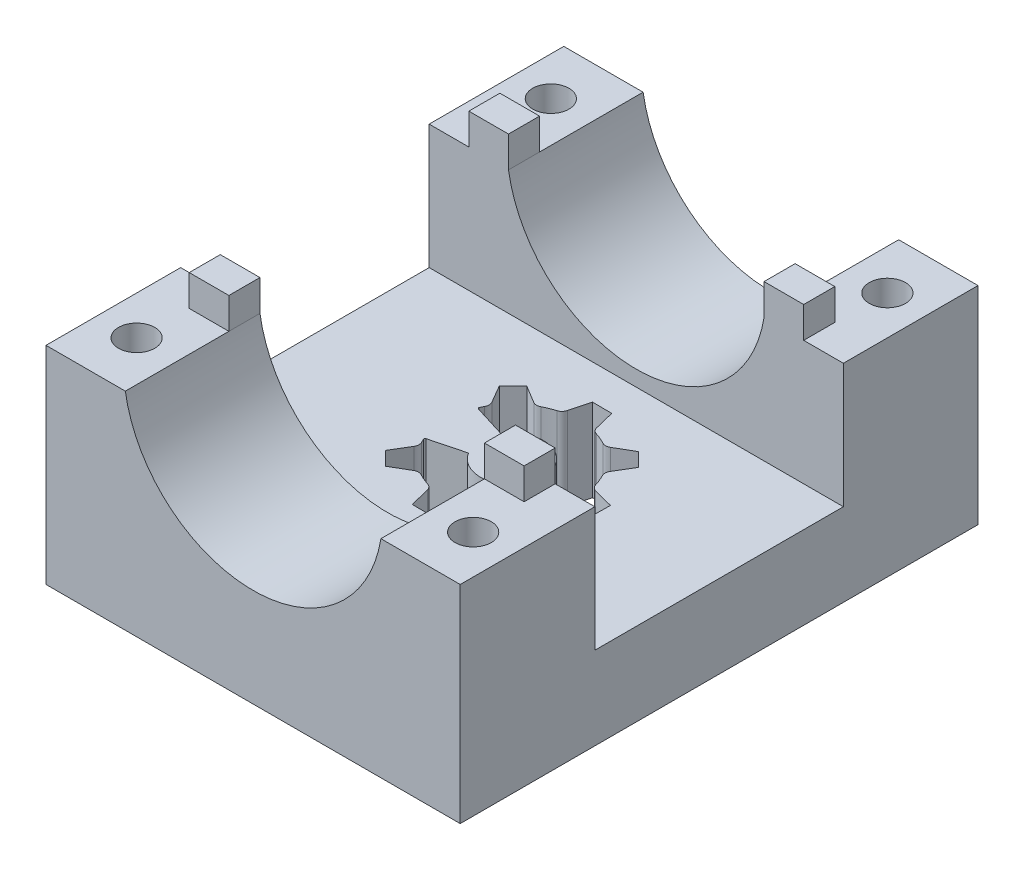
SolidWorks part; units mm, degrees
ref_plane "Alzado" through (0, 0, 0) normal (0, 0, 1) x (1, 0, 0)
ref_plane "Planta" through (0, 0, 0) normal (0, 1, 0) x (1, 0, 0)
ref_plane "Vista lateral" through (0, 0, 0) normal (1, 0, 0) x (0, 0, -1)
sketch "Croquis1" plane through (0, 0, 0) normal (0, 1, 0) x (1, 0, 0)
  line L1 (0, 0) -> (40, 0)
  line L2 (0, 0) -> (0, 50)
  line L3 (0, 50) -> (40, 50)
  line L4 (40, 0) -> (40, 50)
  dimension "D1" = 50
  dimension "D2" = 40
extrude "Saliente-Extruir1" add sketch "Croquis1" along normal blind 20
sketch "Croquis2" plane through (0, 0, 0) normal (0, 0, 1) x (1, 0, 0)
  line L1 (20, 20) -> (20, 22) construction
  line L2 (0, 20) -> (40, 20) construction
  circle A1 centre (20, 22) radius 12.5
  dimension "D1" = 2
  dimension "D2" = 25
extrude "Cortar-Extruir1" cut sketch "Croquis2" against normal through all
sketch "Croquis3" plane through (0, 20, 0) normal (0, 1, 0) x (1, 0, 0)
  line L1 (7.661, 50) -> (0, 50) construction
  line L6 (0, 50) -> (0, 0) construction
  circle A0 centre (3.75, 45) radius 1.75
  circle A1 centre (36.25, 45) radius 1.75
  circle A2 centre (36.25, 5) radius 1.75
  circle A3 centre (3.75, 5) radius 1.75
  dimension "D1" = 5
  dimension "D5" = 3.5
  dimension "D2" = 3.75
  dimension "D3" = 2
  dimension "D4" = 2
extrude "Cortar-Extruir2" cut sketch "Croquis3" against normal through all
sketch "Croquis4" plane through (40, 0, 0) normal (1, 0, 0) x (0, 0, -1)
  line L2 (0, 20) -> (50, 20) construction
  line L3 (25, 20) -> (37, 20)
  line L4 (37, 20) -> (37, 8)
  line L5 (37, 8) -> (13, 8)
  line L6 (13, 8) -> (13, 20)
  line L7 (13, 20) -> (25, 20)
  dimension "D1" = 12
  dimension "D2" = 12
  dimension "D3" = 24
  dimension "D4" = 12
extrude "Cortar-Extruir3" cut sketch "Croquis4" against normal through all
sketch "Croquis5" plane through (0, 20, 0) normal (0, 1, 0) x (1, 0, 0)
  line L16 (7.661, 40) -> (7.661, 37)
  line L17 (3.8305, 37) -> (3.8305, 40)
  line L18 (0, 37) -> (7.661, 37) construction
  line L19 (3.8305, 40) -> (7.661, 40)
  line L22 (7.661, 37) -> (3.8305, 37)
  line L23 (36.1695, 37) -> (36.1695, 40)
  line L24 (32.339, 37) -> (40, 37) construction
  line L25 (36.1695, 40) -> (32.339, 40)
  line L28 (32.339, 37) -> (36.1695, 37)
  line L29 (36.1695, 13) -> (36.1695, 10)
  line L30 (32.339, 13) -> (40, 13) construction
  line L31 (36.1695, 10) -> (32.339, 10)
  line L34 (32.339, 13) -> (36.1695, 13)
  line L35 (3.8305, 10) -> (3.8305, 13)
  line L36 (0, 13) -> (7.661, 13) construction
  line L37 (3.8305, 13) -> (7.661, 13)
  line L40 (7.661, 10) -> (3.8305, 10)
  line L42 (32.339, 40) -> (32.339, 37)
  line L48 (7.661, 37) -> (7.661, 50) construction
  line L50 (32.339, 50) -> (32.339, 37) construction
  line L52 (7.661, 13) -> (7.661, 10)
  line L54 (32.339, 13) -> (32.339, 10)
  dimension "D1" = 3
  dimension "D4" = 3
extrude "Saliente-Extruir3" add sketch "Croquis5" along normal blind 3
sketch "Croquis6" plane through (0, 0, 0) normal (0, -1, 0) x (1, 0, 0)
  line L0 (20, 0) -> (20, -50) construction
  line L1 (13.1881, -19.6153) -> (14.5015, -18.2797)
  line L2 (18.9908, -16.3758) -> (20.864, -16.36)
  line L3 (25.3847, -18.1881) -> (26.7203, -19.5015)
  line L4 (28.6242, -23.9908) -> (28.64, -25.864)
  line L5 (26.8119, -30.3847) -> (25.4985, -31.7203)
  line L6 (14.2096, -27.5521) -> (17.384, -26.5714)
  line L7 (13.1881, -19.6153) -> (14.2199, -21.3215)
  line L8 (21.0092, -33.6242) -> (19.136, -33.64)
  line L9 (14.6153, -31.8119) -> (13.2797, -30.4985)
  line L10 (14.5015, -18.2797) -> (16.2249, -19.2826)
  line L11 (18.9908, -16.3758) -> (18.5139, -18.3118)
  line L12 (20.864, -16.36) -> (21.3734, -18.2878)
  line L13 (25.3847, -18.1881) -> (23.6785, -19.2199)
  line L14 (26.7203, -19.5015) -> (25.7174, -21.2249)
  line L15 (28.6242, -23.9908) -> (26.6882, -23.5139)
  line L16 (28.64, -25.864) -> (26.7122, -26.3734)
  line L17 (26.8119, -30.3847) -> (25.7801, -28.6785)
  line L18 (25.4985, -31.7203) -> (23.7751, -30.7174)
  line L19 (21.0092, -33.6242) -> (21.4861, -31.6882)
  line L20 (19.136, -33.64) -> (18.6266, -31.7122)
  line L21 (14.6153, -31.8119) -> (16.3215, -30.7801)
  line L22 (13.2797, -30.4985) -> (14.2826, -28.7751)
  line L23 (17.4066, -23.3915) -> (14.1706, -22.5477)
  line L24 (0, 0) -> (40, 0) construction
  line L26 (40, -50) -> (0, -50) construction
  line L27 (40, -25) -> (0, -25) construction
  line L28 (40, 0) -> (40, -50) construction
  line L29 (0, -50) -> (0, 0) construction
  arc A0 (21.9667, -31.1744) -> (23.0717, -30.7057) centre (20, -25) ccw
  arc A1 (14.127, -27.7383) -> (14.2943, -28.0717) centre (20, -25) ccw
  arc A2 (14.2096, -27.5521) -> (14.127, -27.7383) centre (14.2495, -27.6812) ccw
  arc A3 (14.0813, -22.3619) -> (14.1706, -22.5477) centre (14.2047, -22.4169) ccw
  arc A4 (16.9283, -19.2943) -> (16.2249, -19.2826) centre (16.587, -18.6603) cw
  arc A5 (14.2434, -22.0247) -> (14.2199, -21.3215) centre (13.6038, -21.6941) ccw
  arc A6 (21.8625, -18.7934) -> (21.3734, -18.2878) centre (22.0695, -18.1038) cw
  arc A7 (18.0333, -18.8256) -> (18.5139, -18.3118) centre (17.8148, -18.1396) ccw
  arc A8 (25.7057, -21.9283) -> (25.7174, -21.2249) centre (26.3397, -21.587) cw
  arc A9 (22.9753, -19.2434) -> (23.6785, -19.2199) centre (23.3059, -18.6038) ccw
  arc A10 (26.2066, -26.8625) -> (26.7122, -26.3734) centre (26.8962, -27.0695) cw
  arc A11 (26.1744, -23.0333) -> (26.6882, -23.5139) centre (26.8604, -22.8148) ccw
  arc A12 (23.0717, -30.7057) -> (23.7751, -30.7174) centre (23.413, -31.3397) cw
  arc A13 (25.7566, -27.9753) -> (25.7801, -28.6785) centre (26.3962, -28.3059) ccw
  arc A14 (18.1375, -31.2066) -> (18.6266, -31.7122) centre (17.9305, -31.8962) cw
  arc A15 (21.9667, -31.1744) -> (21.4861, -31.6882) centre (22.1852, -31.8604) ccw
  arc A16 (14.2943, -28.0717) -> (14.2826, -28.7751) centre (13.6603, -28.413) cw
  arc A17 (17.0247, -30.7566) -> (16.3215, -30.7801) centre (16.6941, -31.3962) ccw
  arc A18 (17.0247, -30.7566) -> (18.1375, -31.2066) centre (20, -25) ccw
  arc A19 (14.2434, -22.0247) -> (14.0813, -22.3619) centre (20, -25) ccw
  arc A20 (18.0333, -18.8256) -> (16.9283, -19.2943) centre (20, -25) ccw
  arc A21 (22.9753, -19.2434) -> (21.8625, -18.7934) centre (20, -25) ccw
  arc A22 (26.1744, -23.0333) -> (25.7057, -21.9283) centre (20, -25) ccw
  arc A23 (25.7566, -27.9753) -> (26.2066, -26.8625) centre (20, -25) ccw
  arc A24 (17.384, -26.5714) -> (17.4066, -23.3915) centre (20, -25) ccw
  dimension "D1" = 0.1351
  dimension "D2" = 0.1351
extrude "Cortar-Extruir5" cut sketch "Croquis6" against normal through all
